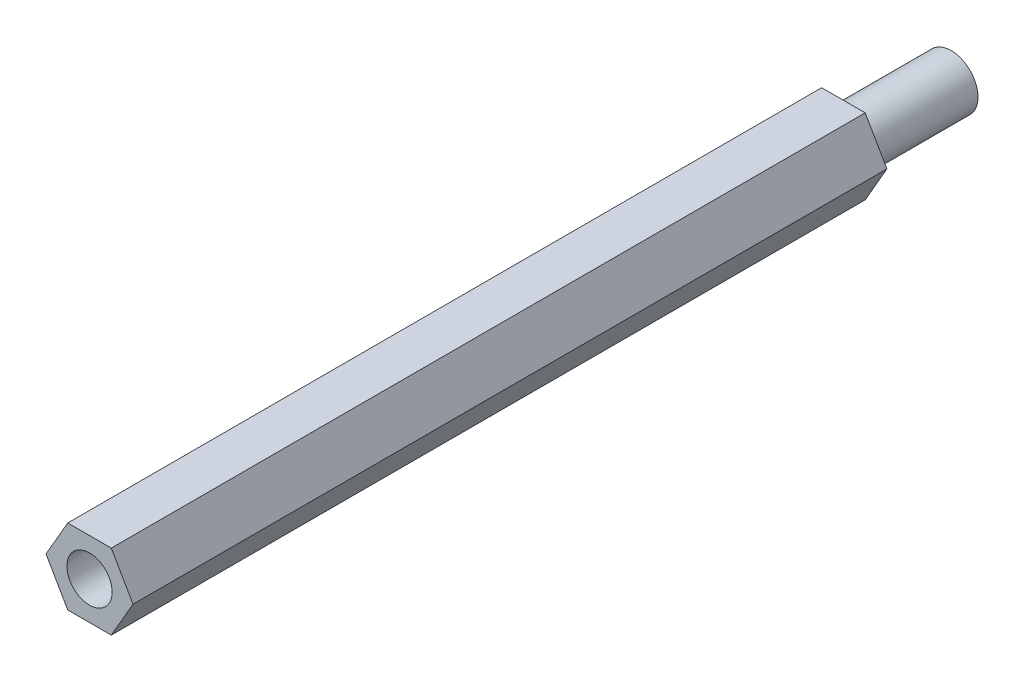
SolidWorks part; units mm, degrees
material "黃銅"
ref_plane "前基準面" through (0, 0, 0) normal (0, 0, 1) x (1, 0, 0)
ref_plane "上基準面" through (0, 0, 0) normal (0, 1, 0) x (1, 0, 0)
ref_plane "右基準面" through (0, 0, 0) normal (1, 0, 0) x (0, 0, -1)
sketch "草圖1" plane through (0, 0, 0) normal (0, 0, 1) x (1, 0, 0)
  line L1 (-2.0207, 3.5) -> (-4.0415, 0)
  line L2 (-4.0415, 0) -> (-2.0207, -3.5)
  line L3 (-2.0207, -3.5) -> (2.0207, -3.5)
  line L4 (2.0207, -3.5) -> (4.0415, 0)
  line L5 (4.0415, 0) -> (2.0207, 3.5)
  line L6 (2.0207, 3.5) -> (-2.0207, 3.5)
  circle A0 centre (0, 0) radius 3.5 construction
  dimension "D1" = 7
extrude "填料-伸長1" add sketch "草圖1" along normal blind 70
sketch "草圖4" plane through (0, 0, 0) normal (0, 0, -1) x (-1, 0, 0)
  circle A0 centre (0, 0) radius 2.5
  dimension "D1" = 5
extrude "填料-伸長2" add sketch "草圖4" along normal blind 10
hole_wizard "M5x0.8 Tapped Hole1" positions "草圖2" profile "草圖3" tap size "M5x0.8" standard "ANSI Metric"
sketch "草圖2" plane through (0, 0, 70) normal (0, 0, 1) x (1, 0, 0)
  point P0 (0, 0)
sketch "草圖3" plane through (0, 0, 70) normal (1, 0, 0) x (0, -1, 0)
  line L0 (0, 0) -> (0, 13.6618)
  line L1 (0, 13.6618) -> (2.1, 12.4)
  line L2 (2.1, 12.4) -> (2.1, 0)
  line L5 (2.1, 0) -> (0, 0)
  line L10 (0, 13.6618) -> (-2.1, 12.4) construction
  line L11 (0, -6.35) -> (0, 107.95) construction
  dimension "螺孔鑽直徑" = 4.2
  dimension "螺孔鑽深度" = 12.4
  dimension "導頭角度" = 118
